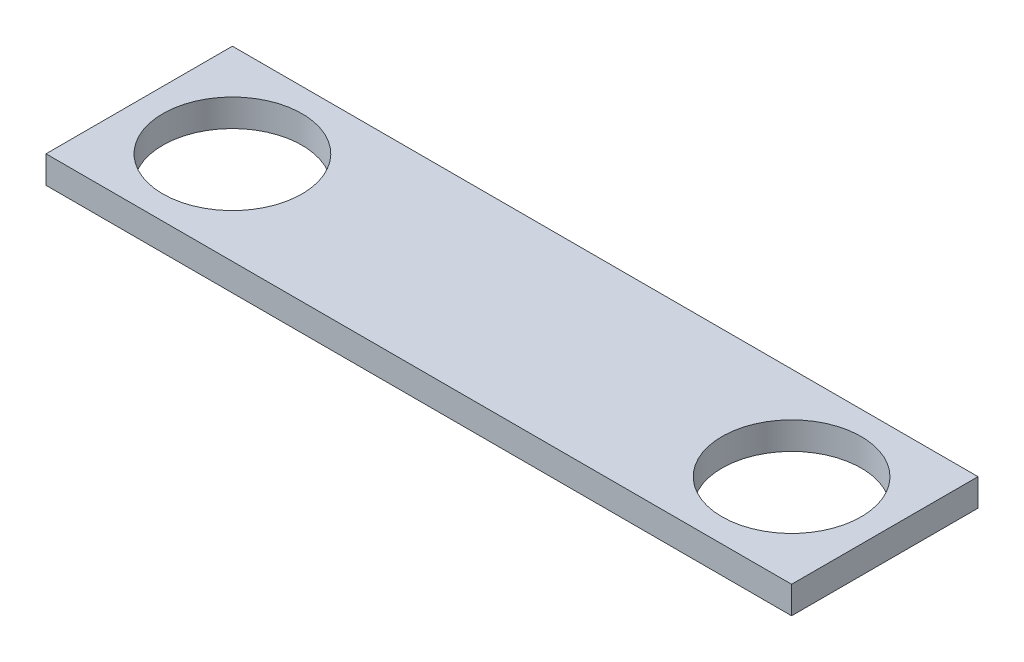
SolidWorks part; units mm, degrees
ref_plane "Front Plane" through (0, 0, 0) normal (0, 0, 1) x (1, 0, 0)
ref_plane "Top Plane" through (0, 0, 0) normal (0, 1, 0) x (1, 0, 0)
ref_plane "Right Plane" through (0, 0, 0) normal (1, 0, 0) x (0, 0, -1)
sketch "Sketch1" plane through (0, 0, 0) normal (0, 1, 0) x (1, 0, 0)
  line L1 (0, 0) -> (152.4, 0)
  line L2 (0, 0) -> (0, 38.1)
  line L3 (0, 38.1) -> (152.4, 38.1)
  line L4 (152.4, 0) -> (152.4, 38.1)
  dimension "D1" = 152.4
  dimension "D2" = 38.1
extrude "Boss-Extrude1" add sketch "Sketch1" along normal blind 5.588
sketch "Sketch6" plane through (0, 5.588, 0) normal (0, 1, 0) x (1, 0, 0)
  line L0 (0, 0) -> (152.4, 0) construction
  line L3 (0, 38.1) -> (0, 0) construction
  circle A0 centre (19.05, 19.05) radius 14.224
  dimension "D1" = 28.448
  dimension "D2" = 19.05
  dimension "D3" = 19.05
extrude "Cut-Extrude4" cut sketch "Sketch6" against normal through all
sketch "Sketch7" plane through (0, 5.588, 0) normal (0, 1, 0) x (1, 0, 0)
  line L0 (0, 0) -> (152.4, 0) construction
  line L1 (152.4, 0) -> (152.4, 38.1) construction
  circle A0 centre (133.35, 19.05) radius 14.224
  dimension "D1" = 28.448
  dimension "D2" = 19.05
  dimension "D3" = 19.05
extrude "Cut-Extrude5" cut sketch "Sketch7" against normal through all
